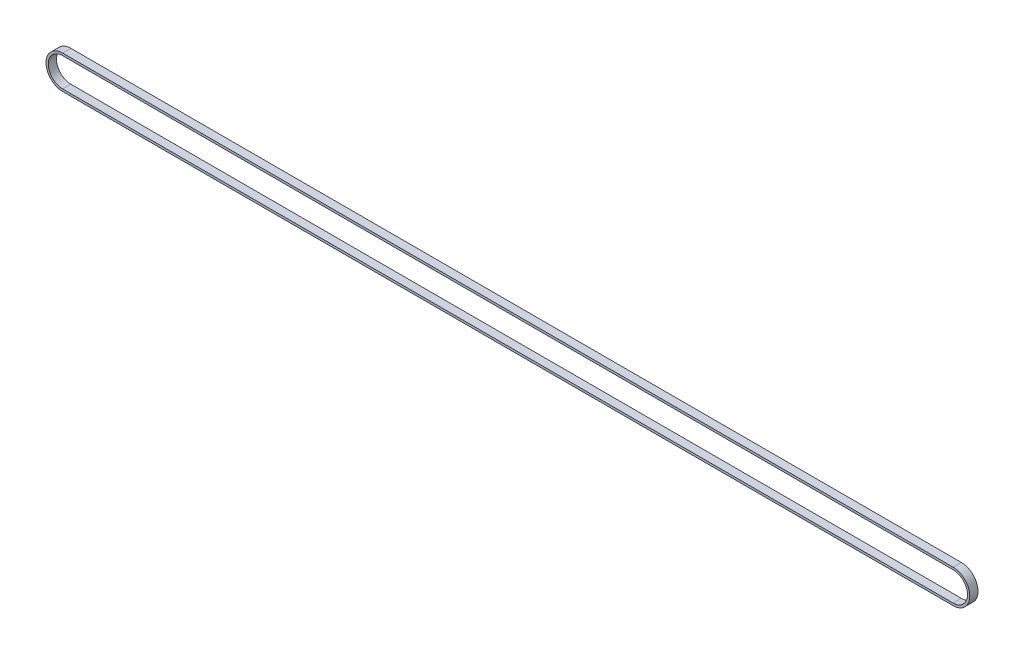
SolidWorks part; units mm, degrees
material "Rubber"
ref_plane "Front Plane" through (0, 0, 0) normal (0, 0, 1) x (1, 0, 0)
ref_plane "Top Plane" through (0, 0, 0) normal (0, 1, 0) x (1, 0, 0)
ref_plane "Right Plane" through (0, 0, 0) normal (1, 0, 0) x (0, 0, -1)
sketch "Sketch1" plane through (0, 0, 0) normal (0, 0, 1) x (1, 0, 0)
  line L0 (0, 0) -> (541, 0) construction
  line L1 (0, 8.75) -> (541, 8.75)
  line L2 (541, -8.75) -> (0, -8.75)
  arc A0 (0, 8.75) -> (0, -8.75) centre (0, 0) ccw
  arc A1 (541, -8.75) -> (541, 8.75) centre (541, 0) ccw
  dimension "D1" = 17.5
  dimension "D2" = 541
extrude "Extrude-Thin1" add sketch "Sketch1" along normal mid plane 5 thin thin type one direction wall 1.38
